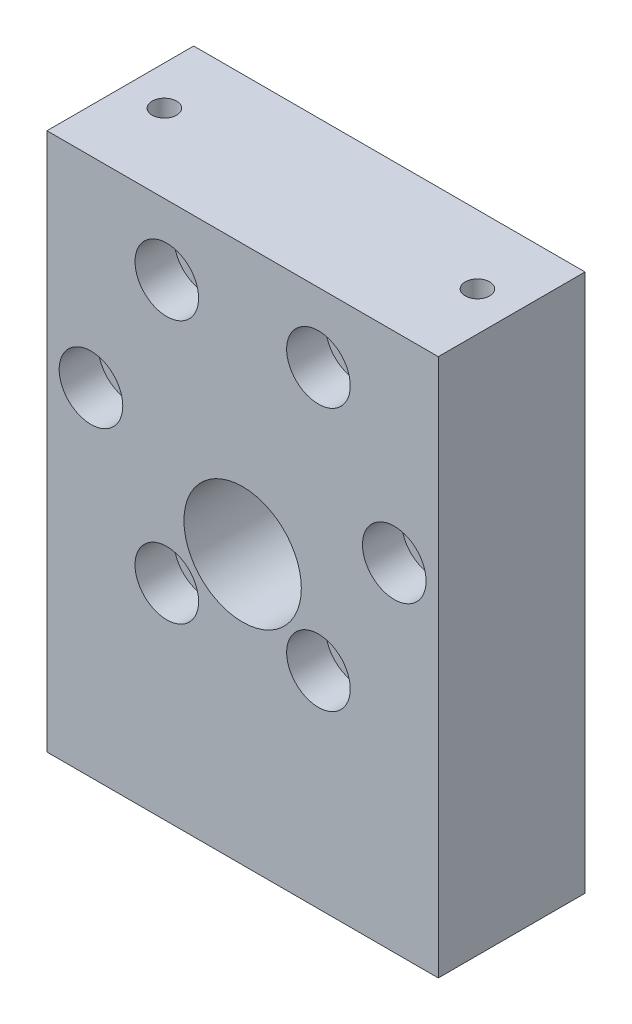
SolidWorks part; units mm, degrees
ref_plane "Front Plane" through (0, 0, 0) normal (0, 0, 1) x (1, 0, 0)
ref_plane "Top Plane" through (0, 0, 0) normal (0, 1, 0) x (1, 0, 0)
ref_plane "Right Plane" through (0, 0, 0) normal (1, 0, 0) x (0, 0, -1)
sketch "Sketch1" plane through (0, 0, 0) normal (0, 0, 1) x (1, 0, 0)
  line L1 (-20, 27.5) -> (20, 27.5)
  line L2 (-20, 27.5) -> (-20, -27.5)
  line L3 (-20, -27.5) -> (20, -27.5)
  line L4 (20, 27.5) -> (20, -27.5)
  line L5 (-20, 27.5) -> (20, -27.5) construction
  line L6 (-20, -27.5) -> (20, 27.5) construction
  circle A0 centre (0, 0) radius 6
  circle A1 centre (15.5, 7) radius 1.5
  circle A2 centre (7.75, -6.4234) radius 1.5
  circle A3 centre (-7.75, -6.4234) radius 1.5
  circle A4 centre (-15.5, 7) radius 1.5
  circle A5 centre (-7.75, 20.4234) radius 1.5
  circle A6 centre (7.75, 20.4234) radius 1.5
  point P0 (0, 0)
  point P8 (0, 7)
  point P24 (0, 7)
  dimension "D3" = 12
  dimension "D5" = 3
  dimension "D1" = 40
  dimension "D2" = 55
  dimension "D4" = 7
  dimension "D6" = 15.5
  dimension "D7" = 6
extrude "Boss-Extrude1" add sketch "Sketch1" along normal blind 15
sketch "Sketch2" plane through (0, 0, 0) normal (0, 0, -1) x (-1, 0, 0)
  line L0 (-15.5, 7) -> (15.5, 7) construction
  line L1 (-7.75, -6.4234) -> (0, 7) construction
  circle A0 centre (0, 7) radius 18.5
  dimension "D1" = 37
extrude "Cut-Extrude1" cut sketch "Sketch2" against normal blind 6
hole_wizard "M3 Tapped Hole1" positions "Sketch4" profile "Sketch3" tap size "M3" standard "ISO"
sketch "Sketch4" plane through (0, -27.5, 0) normal (0, -1, 0) x (-1, 0, 0)
  line L7 (20, 0) -> (-20, 0) construction
  line L8 (20, -15) -> (-20, -15) construction
  line L10 (0, 0) -> (-20, 0) construction
  line L11 (-20, -15) -> (-20, 0) construction
  line L12 (20, -15) -> (20, 0) construction
  point P0 (-10, -7)
  point P4 (10, -7)
  dimension "D1" = 10
  dimension "D2" = 10
  dimension "D3" = 8
  dimension "D4" = 8
sketch "Sketch3" plane through (10, -27.5, 7) normal (1, 0, 0) x (0, 0, -1)
  line L0 (0, 0) -> (0, 10.7511)
  line L1 (0, 10.7511) -> (1.25, 10)
  line L2 (1.25, 10) -> (1.25, 0)
  line L5 (1.25, 0) -> (0, 0)
  line L10 (0, 10.7511) -> (-1.25, 10) construction
  line L11 (0, -6.35) -> (0, 107.95) construction
  dimension "Tap Drill Dia." = 2.5
  dimension "Tap Drill Depth" = 10
  dimension "Drill Angle" = 118
cosmetic thread "Hole Thread1" parameters "D1"=9, "D2"=3
cosmetic thread "Hole Thread3" parameters "D1"=9, "D2"=3
hole_wizard "M3 Tapped Hole2" positions "Sketch6" profile "Sketch5" tap size "M3" standard "ISO"
sketch "Sketch6" plane through (0, 27.5, 0) normal (0, 1, 0) x (1, 0, 0)
  line L10 (20, -15) -> (-20, -15) construction
  line L11 (-20, -15) -> (-20, 0) construction
  line L12 (20, -15) -> (20, 0) construction
  line L13 (0, -15) -> (0, 0) construction
  line L14 (20, 0) -> (-20, 0) construction
  point P0 (-16, -7)
  point P2 (16, -7)
  dimension "D1" = 8
  dimension "D2" = 4
  dimension "D3" = 4
sketch "Sketch5" plane through (-16, 27.5, 7) normal (1, 0, 0) x (0, 0, 1)
  line L0 (0, 0) -> (0, 8.7511)
  line L1 (0, 8.7511) -> (1.25, 8)
  line L2 (1.25, 8) -> (1.25, 0)
  line L5 (1.25, 0) -> (0, 0)
  line L10 (0, 8.7511) -> (-1.25, 8) construction
  line L11 (0, -6.35) -> (0, 107.95) construction
  dimension "Tap Drill Dia." = 2.5
  dimension "Tap Drill Depth" = 8
  dimension "Drill Angle" = 118
cosmetic thread "Hole Thread5" parameters "D1"=7.5, "D2"=3
cosmetic thread "Hole Thread6" parameters "D1"=7.5, "D2"=3
sketch "Sketch7" plane through (0, 0, 15) normal (0, 0, 1) x (1, 0, 0)
  line L0 (15.5, 7) -> (-15.5, 7) construction
  line L1 (7.75, -6.4234) -> (0, 7) construction
  circle A0 centre (-7.75, 20.4234) radius 3.25
  circle A1 centre (7.75, 20.4234) radius 3.25
  circle A2 centre (15.5, 7) radius 3.25
  circle A3 centre (7.75, -6.4234) radius 3.25
  circle A4 centre (-7.75, -6.4234) radius 3.25
  circle A5 centre (-15.5, 7) radius 3.25
  point P22 (0, 7)
  dimension "D1" = 6.5
  dimension "D2" = 6
extrude "Cut-Extrude2" cut sketch "Sketch7" against normal blind 4
sketch "Sketch8" plane through (0, 0, 15) normal (0, 0, 1) x (1, 0, 0)
  circle A0 centre (0, 7) radius 15.5 construction
sketch "Sketch9" plane through (0, 0, 0) normal (0, 0, -1) x (-1, 0, 0)
  line L0 (-18, -25.5) -> (-13.25, -25.5)
  line L1 (-13.25, -25.5) -> (-13.25, -15.5)
  line L3 (-13.25, -15.5) -> (-6.75, -15.5)
  line L4 (-6.75, -15.5) -> (-6.75, -25.5)
  line L5 (-6.75, -25.5) -> (6.75, -25.5)
  line L7 (6.75, -25.5) -> (6.75, -15.5)
  line L8 (6.75, -15.5) -> (13.25, -15.5)
  line L11 (13.25, -15.5) -> (13.25, -25.5)
  line L12 (13.25, -25.5) -> (18, -25.5)
  line L16 (18, -25.5) -> (18, -2.8107)
  line L18 (-18, -2.8107) -> (-18, -25.5)
  line L20 (-20, -27.5) -> (-20, 27.5) construction
  line L21 (20, 27.5) -> (20, -27.5) construction
  line L22 (20, -27.5) -> (-20, -27.5) construction
  line L23 (-8.75, -27.5) -> (-8.75, -17.5) construction
  line L24 (-8.75, -27.5) -> (-8.75, -17.5) construction
  line L25 (11.25, -27.5) -> (11.25, -17.5) construction
  line L26 (11.25, -27.5) -> (11.25, -17.5) construction
  line L27 (8.75, -17.5) -> (11.25, -17.5) construction
  line L28 (-11.25, -17.5) -> (-8.75, -17.5) construction
  circle A0 centre (0, 7) radius 20.5 construction
  circle A1 centre (0, 7) radius 18.5 construction
  arc A2 (-18, -2.8107) -> (18, -2.8107) centre (0, 7) ccw
  dimension "D3" = 2
  dimension "D5" = 2
  dimension "D4" = 4.5
  dimension "D1" = 2
  dimension "D7" = 2
  dimension "D8" = 2
  dimension "D9" = 2
  dimension "D6" = 4.5
  dimension "D2" = 2
  dimension "D10" = 2
extrude "Cut-Extrude3" cut sketch "Sketch9" against normal blind 12
fillet "Fillet1" radius 2 12 edges at (18, -25.5, 6) (13.25, -25.5, 6) (13.25, -15.5, 6) (6.75, -25.5, 6) (6.75, -15.5, 6) (18, -2.8107, 6) (-18, -2.8107, 6) (-18, -25.5, 6) (-13.25, -25.5, 6) (-13.25, -15.5, 6) (-6.75, -15.5, 6) (-6.75, -25.5, 6)
sketch "Sketch10" plane through (0, 0, 15) normal (0, 0, 1) x (1, 0, 0)
  line L0 (-20, 27.5) -> (-23, 27.5)
  line L1 (-23, 27.5) -> (-23, -20.5)
  line L2 (-23, -20.5) -> (-20, -20.5)
  line L3 (-20, 27.5) -> (-20, -27.5) construction
  line L4 (-20, -20.5) -> (-20, 27.5)
  line L5 (20, 27.5) -> (20, -20.5)
  line L6 (20, -27.5) -> (20, 27.5) construction
  line L7 (20, -20.5) -> (23, -20.5)
  line L8 (23, -20.5) -> (23, 27.5)
  line L9 (23, 27.5) -> (20, 27.5)
  line L10 (-20, -27.5) -> (20, -27.5) construction
  dimension "D1" = 3
  dimension "D2" = 3
  dimension "D3" = 7
extrude "Boss-Extrude2" add sketch "Sketch10" against normal blind 15
